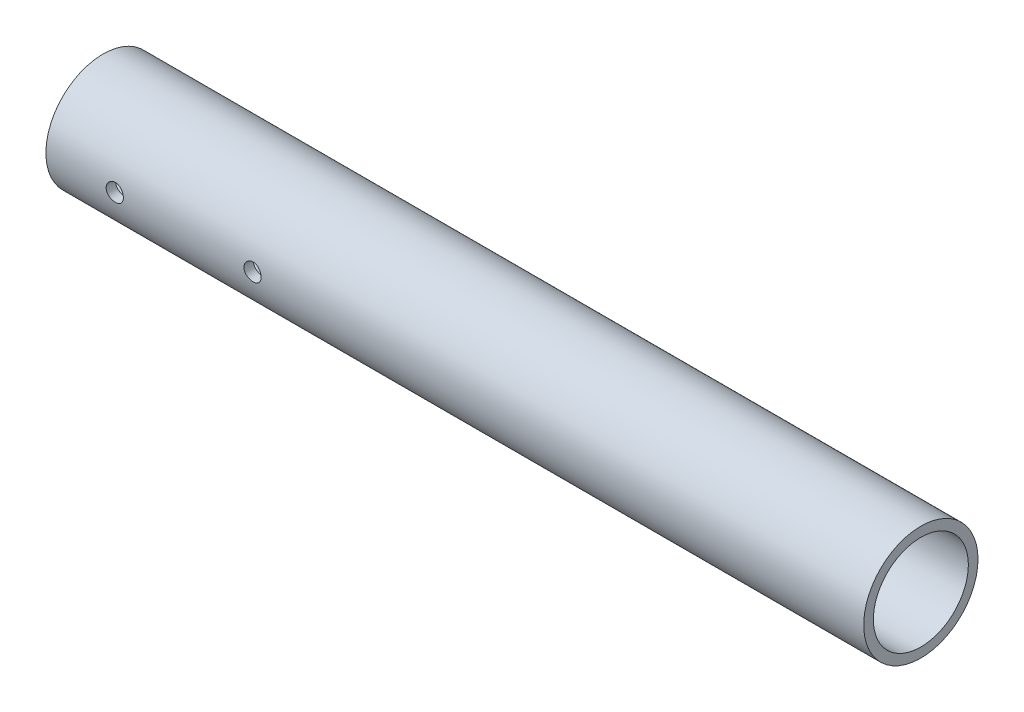
SolidWorks part; units mm, degrees
material "6061-T6 (SS)"
ref_plane "Front Plane" through (0, 0, 0) normal (0, 0, 1) x (1, 0, 0)
ref_plane "Top Plane" through (0, 0, 0) normal (0, 1, 0) x (1, 0, 0)
ref_plane "Right Plane" through (0, 0, 0) normal (1, 0, 0) x (0, 0, -1)
sketch "Sketch1" plane through (0, 0, 0) normal (1, 0, 0) x (0, 0, -1)
  circle A0 centre (0, 0) radius 21.082
  circle A1 centre (0, 0) radius 17.526
  dimension "D1" = 42.164
  dimension "D2" = 35.052
extrude "Boss-Extrude1" add sketch "Sketch1" along normal blind 127 and the other way blind 174.625
sketch "Sketch2" plane through (0, 0, 0) normal (0, 0, 1) x (1, 0, 0)
  line L0 (-174.625, 21.082) -> (-174.625, -21.082) construction
  circle A0 centre (-98.425, 0) radius 3.175
  circle A1 centre (-149.225, 0) radius 3.175
  dimension "D1" = 6.35
  dimension "D2" = 25.4
  dimension "D3" = 50.8
extrude "Cut-Extrude1" cut sketch "Sketch2" against normal through all both and the other way through all
